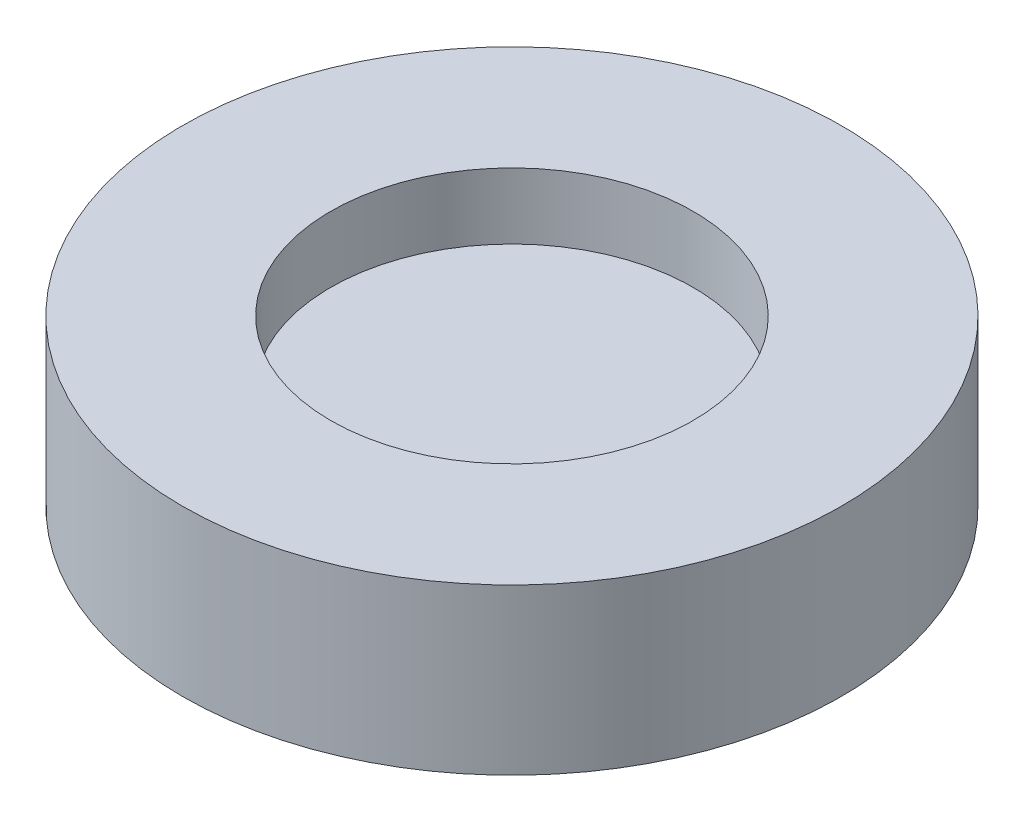
SolidWorks part; units mm, degrees
ref_plane "Front Plane" through (0, 0, 0) normal (0, 0, 1) x (1, 0, 0)
ref_plane "Top Plane" through (0, 0, 0) normal (0, 1, 0) x (1, 0, 0)
ref_plane "Right Plane" through (0, 0, 0) normal (1, 0, 0) x (0, 0, -1)
sketch "Sketch1" plane through (0, 0, 0) normal (0, 1, 0) x (1, 0, 0)
  circle A0 centre (0, 0) radius 10
  dimension "D1" = 20
extrude "Boss-Extrude1" add sketch "Sketch1" along normal blind 5
sketch "Sketch2" plane through (0, 5, 0) normal (0, 1, 0) x (1, 0, 0)
  circle A0 centre (0, 0) radius 5.5
  dimension "D1" = 11
extrude "Cut-Extrude1" cut sketch "Sketch2" against normal blind 2
sketch "Sketch3" plane through (0, 0, 0) normal (0, -1, 0) x (1, 0, 0)
  circle A0 centre (0, 0) radius 1.25
  dimension "D1" = 2.5
extrude "Cut-Extrude2" cut sketch "Sketch3" against normal blind 2.5
fillet "Fillet1" radius 1 1 edges at (0, 2.5, -1.25)
